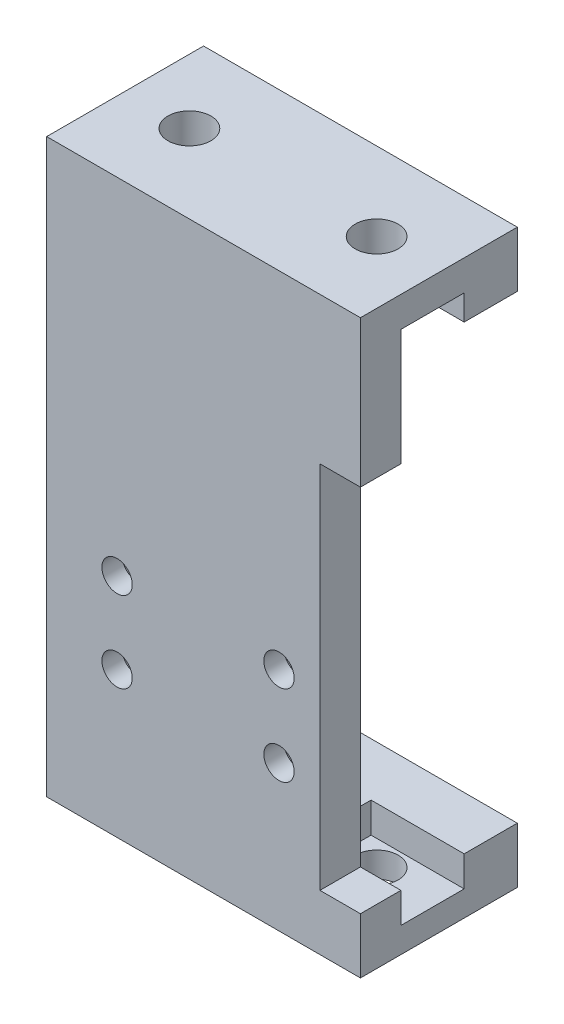
SolidWorks part; units mm, degrees
ref_plane "Front Plane" through (0, 0, 0) normal (0, 0, 1) x (1, 0, 0)
ref_plane "Top Plane" through (0, 0, 0) normal (0, 1, 0) x (1, 0, 0)
ref_plane "Right Plane" through (0, 0, 0) normal (1, 0, 0) x (0, 0, -1)
sketch "Sketch1" plane through (0, 0, 0) normal (0, 0, 1) x (1, 0, 0)
  line L0 (0, 51) -> (31, 51)
  line L1 (14.9527, 16.8756) -> (14.9527, 8.8756) construction
  line L2 (31, 36.5) -> (31, 51)
  line L6 (0, 0) -> (27, 0)
  line L7 (24.1651, 18.9756) -> (21.7402, 18.9756)
  line L8 (21.7402, 18.9756) -> (20.5278, 16.8756)
  line L9 (0, 51) -> (0, 0)
  line L10 (20.5278, 16.8756) -> (21.7402, 14.7756)
  line L11 (21.7402, 14.7756) -> (24.1651, 14.7756)
  line L12 (27, 36.5) -> (31, 36.5)
  line L13 (24.1651, 14.7756) -> (25.3775, 16.8756)
  line L14 (25.3775, 16.8756) -> (24.1651, 18.9756)
  line L21 (24.1651, 10.9756) -> (21.7402, 10.9756)
  line L22 (21.7402, 10.9756) -> (20.5278, 8.8756)
  line L23 (20.5278, 8.8756) -> (21.7402, 6.7756)
  line L24 (21.7402, 6.7756) -> (24.1651, 6.7756)
  line L25 (24.1651, 6.7756) -> (25.3775, 8.8756)
  line L26 (25.3775, 8.8756) -> (24.1651, 10.9756)
  line L27 (8.1651, 18.9756) -> (5.7402, 18.9756)
  line L28 (5.7402, 18.9756) -> (4.5278, 16.8756)
  line L29 (4.5278, 16.8756) -> (5.7402, 14.7756)
  line L30 (5.7402, 14.7756) -> (8.1651, 14.7756)
  line L31 (8.1651, 14.7756) -> (9.3775, 16.8756)
  line L32 (9.3775, 16.8756) -> (8.1651, 18.9756)
  line L33 (8.1651, 10.9756) -> (5.7402, 10.9756)
  line L34 (5.7402, 10.9756) -> (4.5278, 8.8756)
  line L35 (4.5278, 8.8756) -> (5.7402, 6.7756)
  line L36 (5.7402, 6.7756) -> (8.1651, 6.7756)
  line L45 (27, 36.5) -> (27, 0)
  line L46 (8.1651, 6.7756) -> (9.3775, 8.8756)
  line L47 (9.3775, 8.8756) -> (8.1651, 10.9756)
  circle A0 centre (22.9527, 16.8756) radius 2.1 construction
  circle A1 centre (22.9527, 8.8756) radius 2.1 construction
  circle A2 centre (6.9527, 8.8756) radius 2.1 construction
  circle A3 centre (6.9527, 16.8756) radius 2.1 construction
  circle A4 centre (22.9527, 16.8756) radius 2.1 construction
  circle A5 centre (22.9527, 8.8756) radius 2.1 construction
  circle A6 centre (6.9527, 16.8756) radius 2.1 construction
  circle A7 centre (6.9527, 8.8756) radius 2.1 construction
  dimension "D1" = 4.2
  dimension "D2" = 27
  dimension "D7" = 51
  dimension "D8" = 36.5
  dimension "D9" = 4
extrude "Boss-Extrude1" add sketch "Sketch1" along normal blind 4
sketch "Sketch2" plane through (0, 0, 4) normal (0, 0, 1) x (1, 0, 0)
  line L0 (0, 51) -> (31, 51)
  line L1 (14.9527, 16.8756) -> (14.9527, 8.8756) construction
  line L2 (31, 51) -> (31, 36.5)
  line L3 (9.9527, 16.8756) -> (8.4527, 19.4737) construction
  line L4 (8.4527, 14.2776) -> (9.9527, 16.8756) construction
  line L5 (0, -2) -> (27, -2)
  line L6 (0, 51) -> (0, -2)
  line L7 (8.4527, 14.2776) -> (5.4527, 19.4737) construction
  line L8 (5.4527, 19.4737) -> (3.9527, 16.8756) construction
  line L9 (8.4527, 19.4737) -> (5.4527, 19.4737) construction
  line L10 (8.4527, 19.4737) -> (5.4527, 14.2776) construction
  line L11 (5.4527, 14.2776) -> (8.4527, 14.2776) construction
  line L12 (3.9527, 16.8756) -> (5.4527, 14.2776) construction
  line L13 (25.9527, 16.8756) -> (24.4527, 19.4737) construction
  line L14 (24.4527, 14.2776) -> (25.9527, 16.8756) construction
  line L15 (24.4527, 14.2776) -> (21.4527, 19.4737) construction
  line L16 (21.4527, 19.4737) -> (19.9527, 16.8756) construction
  line L17 (24.4527, 19.4737) -> (21.4527, 19.4737) construction
  line L18 (24.4527, 19.4737) -> (21.4527, 14.2776) construction
  line L19 (21.4527, 14.2776) -> (24.4527, 14.2776) construction
  line L20 (19.9527, 16.8756) -> (21.4527, 14.2776) construction
  line L21 (25.9527, 8.8756) -> (24.4527, 11.4737) construction
  line L22 (24.4527, 6.2776) -> (25.9527, 8.8756) construction
  line L23 (24.4527, 6.2776) -> (21.4527, 11.4737) construction
  line L24 (21.4527, 11.4737) -> (19.9527, 8.8756) construction
  line L25 (24.4527, 11.4737) -> (21.4527, 11.4737) construction
  line L26 (24.4527, 11.4737) -> (21.4527, 6.2776) construction
  line L27 (21.4527, 6.2776) -> (24.4527, 6.2776) construction
  line L28 (19.9527, 8.8756) -> (21.4527, 6.2776) construction
  line L29 (9.9527, 8.8756) -> (8.4527, 11.4737) construction
  line L30 (8.4527, 6.2776) -> (9.9527, 8.8756) construction
  line L31 (8.4527, 6.2776) -> (5.4527, 11.4737) construction
  line L32 (5.4527, 11.4737) -> (3.9527, 8.8756) construction
  line L33 (8.4527, 11.4737) -> (5.4527, 11.4737) construction
  line L34 (8.4527, 11.4737) -> (5.4527, 6.2776) construction
  line L35 (5.4527, 6.2776) -> (8.4527, 6.2776) construction
  line L36 (3.9527, 8.8756) -> (5.4527, 6.2776) construction
  line L37 (31, 36.5) -> (27, 36.5)
  line L40 (27, 36.5) -> (27, -2)
  circle A0 centre (22.9527, 16.8756) radius 1.5
  circle A1 centre (22.9527, 8.8756) radius 1.5
  circle A2 centre (6.9527, 8.8756) radius 1.5
  circle A3 centre (6.9527, 16.8756) radius 1.5
  dimension "D1" = 3
  dimension "D2" = 3
  dimension "D3" = 3
  dimension "D4" = 3
  dimension "D5" = 3
  dimension "D6" = 27
  dimension "D7" = 53
extrude "Boss-Extrude2" add sketch "Sketch2" against normal blind 2
sketch "Sketch3" plane through (0, 51, 0) normal (0, 1, 0) x (1, 0, 0)
  line L0 (10.9, 0) -> (20.3, 0)
  line L1 (21.8, 1.5) -> (21.8, 6.25)
  line L2 (1.8, 6.25) -> (0, 6.25)
  line L3 (21.8, 6.25) -> (31, 6.25)
  line L4 (0, 11.25) -> (0, 11.5)
  line L5 (1.8, 6.25) -> (9.4, 6.25)
  line L6 (31, 6.25) -> (31, 11.5)
  line L7 (9.4, 6.25) -> (9.4, 1.5)
  line L8 (15.6, 4.2247) -> (15.6, 0) construction
  line L9 (20.3, 0) -> (21.8, 1.5)
  line L10 (10.9, 0) -> (9.4, 1.5)
  line L11 (0, 6.25) -> (0, 11.25)
  line L12 (0, 11.5) -> (31, 11.5)
extrude "Boss-Extrude3" add sketch "Sketch3" against normal blind 5.5
sketch "Sketch4" plane through (0, 51, 0) normal (0, 1, 0) x (1, 0, 0)
  line L0 (1.8, 11.5) -> (27, 11.5) construction
  line L1 (21.8, -2.55) -> (23.5, -2.55) construction
  line L2 (21.8, 0) -> (21.8, -5.1) construction
  line L3 (15.6, 10.5) -> (15.6, -23.2755) construction
  line L4 (3.1, 5.25) -> (3.1, 15.75) construction
  line L5 (28.1, 10.5) -> (3.1, 10.5) construction
  line L6 (28.1, 5.25) -> (28.1, 15.75) construction
  line L7 (31, 10.5) -> (28.1, 10.5) construction
  line L8 (31, 5.25) -> (1.8, 5.25) construction
  line L9 (9.4, -7.75) -> (21.8, -7.75) construction
  line L10 (31, 0) -> (1.8, 0) construction
  line L11 (31, -10.75) -> (1.8, -10.75) construction
  line L12 (1.8, 0) -> (1.8, 5.25) construction
  line L13 (1.8, 0) -> (1.8, -10.75) construction
  line L14 (1.8, 15.75) -> (31, 15.75) construction
  line L15 (31, 5.25) -> (31, 0) construction
  line L16 (1.8, 11.5) -> (1.8, 5.25) construction
  line L17 (31, 0) -> (31, -10.75) construction
  line L18 (27, 11.5) -> (31, 5.25) construction
  line L19 (31, -4) -> (0, -4)
  line L20 (0, -4) -> (0, 11.5)
  line L21 (0, 11.5) -> (31, 11.5)
  line L22 (31, -4) -> (31, 0)
  line L24 (31, 11.5) -> (31, 0)
  circle A0 centre (7.7, -2.55) radius 1.85 construction
  circle A1 centre (23.5, -2.55) radius 1.85 construction
  circle A2 centre (6.35, 3.75) radius 2.125
  circle A3 centre (24.85, 3.75) radius 2.125
  point P32 (15.6, -7.75)
  dimension "D1" = 4.25
extrude "Boss-Extrude4" add sketch "Sketch4" against normal blind 3
sketch "Sketch5" [suppressed] plane through (0, 51.6512, 0) normal (0, -1, 0) x (1, 0, 0)
  line L0 (0, -11.5) -> (0, 6) construction
  line L1 (0, 6) -> (31, 6) construction
  line L2 (31, 6) -> (31, -11.5) construction
  line L3 (31, -11.5) -> (0, -11.5) construction
  line L4 (0, -6.25) -> (9.4, -6.25) construction
  line L5 (9.4, -6.25) -> (9.4, -1.5) construction
  line L6 (9.4, -1.5) -> (10.9, 0) construction
  line L7 (10.9, 0) -> (20.3, 0) construction
  line L8 (20.3, 0) -> (21.8, -1.5) construction
  line L9 (21.8, -1.5) -> (21.8, -6.25) construction
  line L10 (21.8, -6.25) -> (31, -6.25) construction
  line L11 (31, -6.25) -> (31, -11.5) construction
  line L12 (31, -11.5) -> (0, -11.5) construction
  line L13 (0, -11.5) -> (0, -6.25) construction
  circle A0 centre (6.35, -3.75) radius 2.1551 construction
  circle A1 centre (24.85, -3.75) radius 2.125 construction
sketch "Sketch6" plane through (0, 0, 0) normal (0, -1, 0) x (1, 0, 0)
  line L0 (0, -11.5) -> (0, 4)
  line L1 (31, 4) -> (0, 4)
  line L2 (31, 4) -> (31, -11.5)
  line L3 (31, -11.5) -> (0, -11.5)
  circle A0 centre (6.35, -3.75) radius 2.1551
  circle A1 centre (24.85, -3.75) radius 2.125
extrude "Boss-Extrude5" add sketch "Sketch6" along normal blind 5.5
sketch "Sketch7" plane through (0, 0, 0) normal (0, -1, 0) x (1, 0, 0)
  line L0 (10.9, 0) -> (0, 0)
  line L1 (0, 0) -> (0, -6.25)
  line L2 (20.3, 0) -> (31, 0)
  line L3 (31, -11.5) -> (0, -11.5) construction
  line L4 (0, -6.25) -> (9.4, -6.25)
  line L5 (9.4, -6.25) -> (9.4, -1.5)
  line L6 (9.4, -1.5) -> (10.9, 0)
  line L8 (20.3, 0) -> (21.8, -1.5)
  line L9 (21.8, -1.5) -> (21.8, -6.25)
  line L10 (21.8, -6.25) -> (31, -6.25)
  line L11 (31, -6.25) -> (31, -11.5) construction
  line L12 (31, -11.5) -> (0, -11.5) construction
  line L13 (0, -11.5) -> (0, -6.25) construction
  line L14 (31, 0) -> (31, -6.25)
extrude "Cut-Extrude4" cut sketch "Sketch7" along normal blind 3
